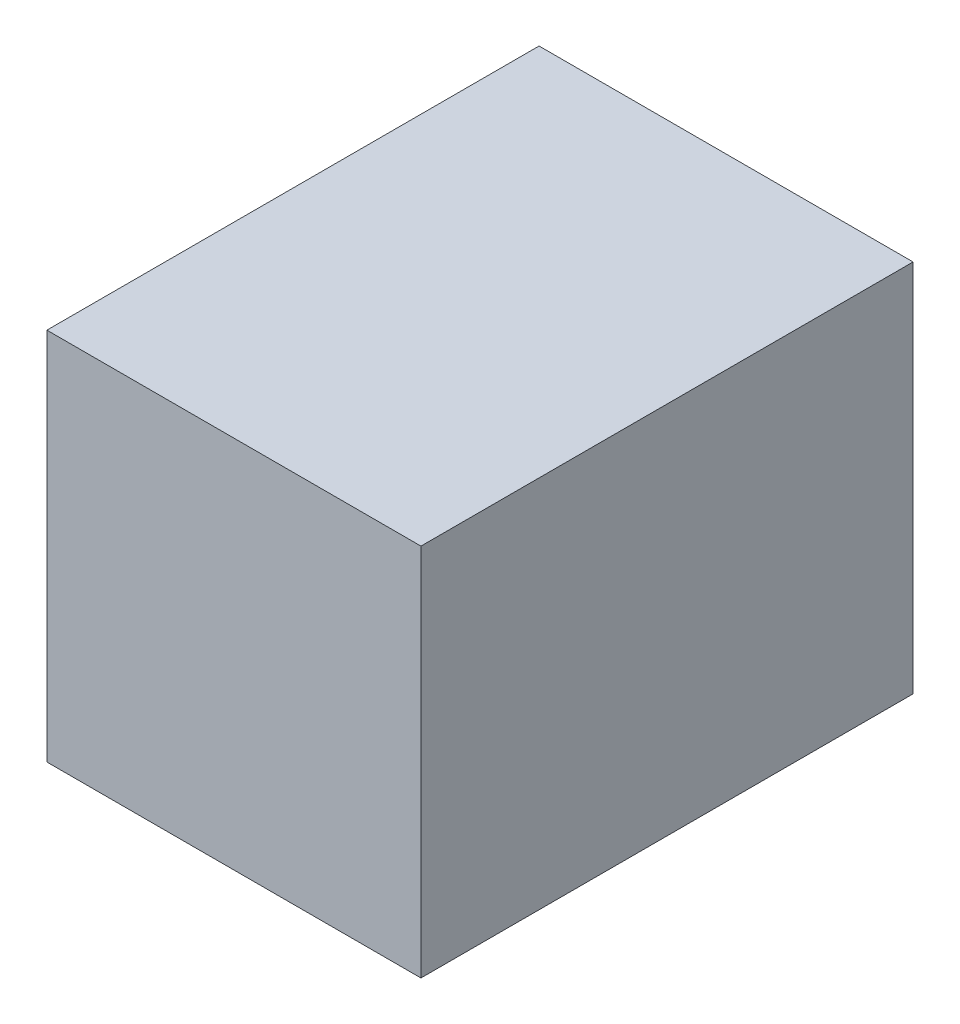
SolidWorks part; units mm, degrees
ref_plane "Front Plane" through (0, 0, 0) normal (0, 0, 1) x (1, 0, 0)
ref_plane "Top Plane" through (0, 0, 0) normal (0, 1, 0) x (1, 0, 0)
ref_plane "Right Plane" through (0, 0, 0) normal (1, 0, 0) x (0, 0, -1)
sketch "Sketch1" plane through (0, 0, 0) normal (0, 0, 1) x (1, 0, 0)
  line L8 (-240.5, 210) -> (-240.5, 229)
  line L9 (-240.5, 229) -> (-259.5, 229)
  line L10 (-259.5, 229) -> (-259.5, 210)
  line L11 (-259.5, 210) -> (-240.5, 210)
extrude "Boss-Extrude1" add sketch "Sketch1" along normal mid plane 25
